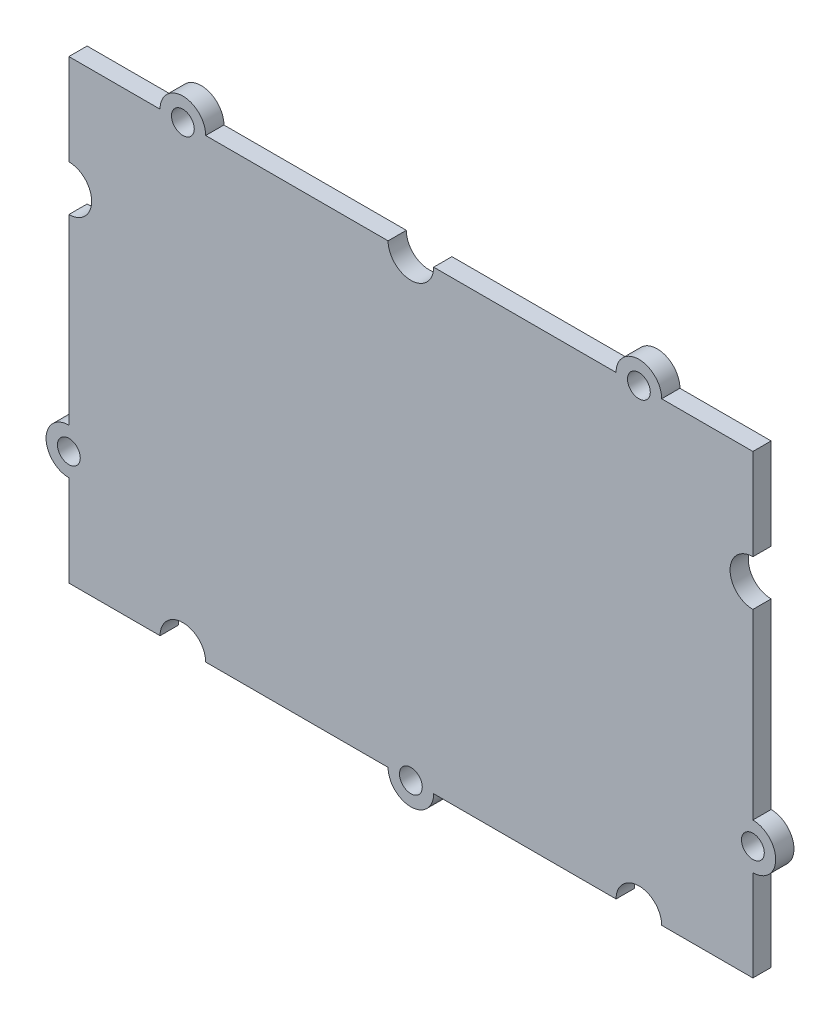
SolidWorks part; units mm, degrees
ref_plane "Plan de face" through (0, 0, 0) normal (0, 0, 1) x (1, 0, 0)
ref_plane "Plan de dessus" through (0, 0, 0) normal (0, 1, 0) x (1, 0, 0)
ref_plane "Plan de droite" through (0, 0, 0) normal (1, 0, 0) x (0, 0, -1)
sketch "Esquisse1" plane through (0, 0, 0) normal (0, 0, 1) x (1, 0, 0)
  line L0 (-44.9151, 0) -> (43.4881, 0) construction
  line L1 (0, -31.1509) -> (0, 34.1028) construction
  line L2 (-30, 8) -> (-30, -8)
  line L3 (-30, 20) -> (-22, 20)
  line L4 (-30, 20) -> (-30, 12)
  line L5 (-30, -20) -> (-22, -20)
  line L6 (30, 20) -> (30, 12)
  line L7 (-30, -12) -> (-30, -20)
  line L8 (-18, -20) -> (-2, -20)
  line L9 (2, -20) -> (18, -20)
  line L10 (22, -20) -> (30, -20)
  line L11 (30, -12) -> (30, -20)
  line L12 (30, 8) -> (30, -8)
  line L13 (22, 20) -> (30, 20)
  line L14 (-18, 20) -> (-2, 20)
  line L15 (2, 20) -> (18, 20)
  arc A0 (-2, 20) -> (2, 20) centre (0, 20) ccw
  arc A1 (22, 20) -> (18, 20) centre (20, 20) ccw
  arc A2 (-18, 20) -> (-22, 20) centre (-20, 20) ccw
  arc A3 (30, 12) -> (30, 8) centre (30, 10) ccw
  arc A4 (30, -12) -> (30, -8) centre (30, -10) ccw
  arc A5 (18, -20) -> (22, -20) centre (20, -20) cw
  arc A6 (2, -20) -> (-2, -20) centre (0, -20) cw
  arc A7 (-22, -20) -> (-18, -20) centre (-20, -20) cw
  arc A8 (-30, -12) -> (-30, -8) centre (-30, -10) cw
  arc A9 (-30, 12) -> (-30, 8) centre (-30, 10) cw
  circle A10 centre (-20, 20) radius 1
  circle A11 centre (20, 20) radius 1
  circle A12 centre (0, -20) radius 1
  circle A13 centre (-30, -10) radius 1
  circle A14 centre (30, -10) radius 1
  dimension "D3" = 20
  dimension "D7" = 4
  dimension "D8" = 4
  dimension "D9" = 4
  dimension "D10" = 4
  dimension "D11" = 4
  dimension "D12" = 2
  dimension "D13" = 2
  dimension "D14" = 2
  dimension "D15" = 2
  dimension "D16" = 2
  dimension "D1" = 60
  dimension "D2" = 40
  dimension "D4" = 20
  dimension "D5" = 10
  dimension "D6" = 10
extrude "Boss.-Extru.1" add sketch "Esquisse1" along normal blind 1.6
